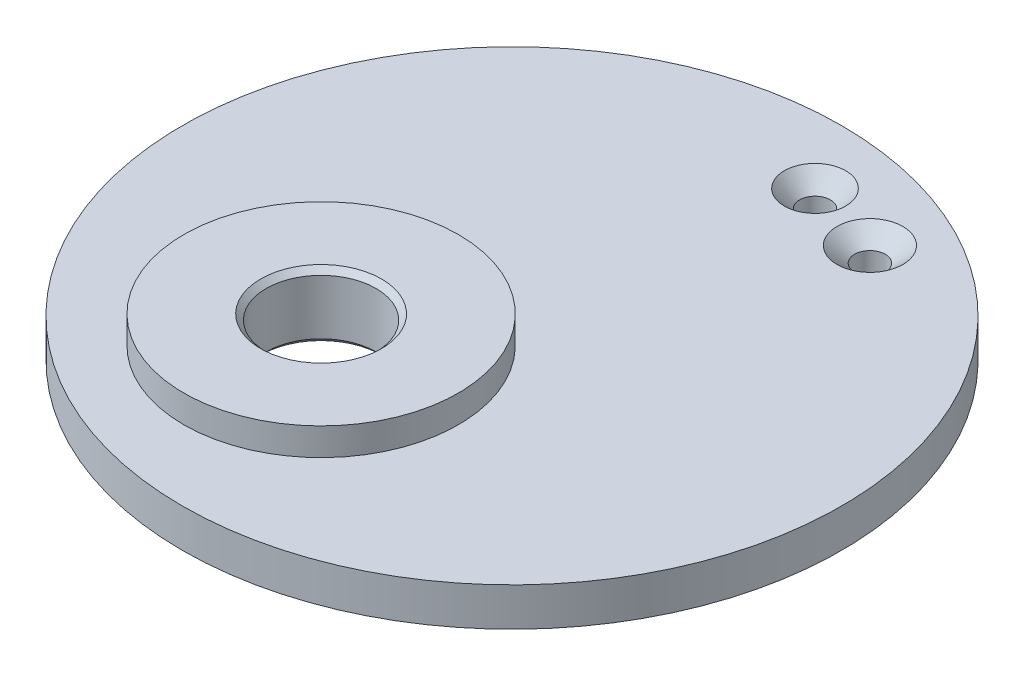
SolidWorks part; units mm, degrees
material "ABS"
ref_plane "Front" through (0, 0, 0) normal (0, 0, 1) x (1, 0, 0)
ref_plane "Top" through (0, 0, 0) normal (0, 1, 0) x (1, 0, 0)
ref_plane "Right" through (0, 0, 0) normal (1, 0, 0) x (0, 0, -1)
sketch "Sketch1" plane through (0, 0, 0) normal (0, 1, 0) x (1, 0, 0)
  circle A0 centre (0, 0) radius 38.1
  dimension "D1" = 76.2
extrude "Boss-Extrude1" add sketch "Sketch1" along normal blind 4.445
sketch "Sketch2" plane through (0, 4.445, 0) normal (0, 1, 0) x (1, 0, 0)
  circle A1 centre (-8.06, -14.01) radius 14.4145
  circle A6 centre (4.76, 30.27) radius 1.778
  circle A7 centre (13.65, 27.73) radius 1.778
  dimension "D1" = 27.73
  dimension "D3" = 3.556
  dimension "D6" = 3.556
  dimension "D9" = 28.829
  dimension "D2" = 13.65
  dimension "D4" = 30.27
  dimension "D5" = 4.76
  dimension "D7" = 14.01
  dimension "D8" = 8.06
extrude "Cut-Extrude1" cut sketch "Sketch2" against normal through all both and the other way through all
sketch "Sketch3" plane through (0, 0, 0) normal (0, -1, 0) x (1, 0, 0)
  arc A0 (4.76, -30.27) -> (13.65, -27.73) centre (7.3136, -22.3803) ccw construction
  arc A1 (3.1957, -35.1031) -> (17.5316, -31.0072) centre (7.3136, -22.3803) ccw
  arc A2 (6.3243, -25.4369) -> (9.7684, -24.4528) centre (7.3136, -22.3803) ccw
  arc A3 (6.3243, -25.4369) -> (3.1957, -35.1031) centre (4.76, -30.27) ccw
  arc A4 (17.5316, -31.0072) -> (9.7684, -24.4528) centre (13.65, -27.73) ccw
  point P3 (9.5918, -30.3539)
  dimension "D1" = 5.08
extrude "Cut-Extrude2" [suppressed] cut sketch "Sketch3" against normal blind 1.905
sketch "Sketch8" plane through (0, 4.445, 0) normal (0, 1, 0) x (1, 0, 0)
  line L0 (0, 0) -> (0, -38.1) construction
  line L1 (-13.97, -38.1) -> (13.97, -38.1)
  line L2 (-13.97, -38.1) -> (-13.97, -64.008)
  line L3 (-13.97, -64.008) -> (13.97, -64.008)
  line L4 (13.97, -38.1) -> (13.97, -64.008)
  line L5 (-20.32, -70.358) -> (-20.32, -32.229)
  line L6 (-20.32, -32.229) -> (20.32, -32.229)
  line L7 (20.32, -32.229) -> (20.32, -70.358)
  line L8 (20.32, -70.358) -> (-20.32, -70.358)
  circle A0 centre (0, 0) radius 38.1 construction
  dimension "D1" = 27.94
  dimension "D2" = 25.908
  dimension "D3" = 6.35
  dimension "D4" = 6.35
extrude "Boss-Extrude4" [suppressed] add sketch "Sketch8" against normal up to surface (6.35 mm away)
fillet "Fillet4" [suppressed] radius 6.35
sketch "Sketch9" plane through (0, 4.445, 0) normal (0, 1, 0) x (1, 0, 0)
  line L0 (22.86, -6.35) -> (22.86, -16.51) construction
  line L1 (27.6225, -6.35) -> (27.6225, -16.51)
  line L2 (18.0975, -6.35) -> (18.0975, -16.51)
  arc A0 (27.6225, -6.35) -> (18.0975, -6.35) centre (22.86, -6.35) ccw
  arc A1 (18.0975, -16.51) -> (27.6225, -16.51) centre (22.86, -16.51) ccw
  point P2 (22.86, -11.43)
  dimension "D1" = 9.525
  dimension "D2" = 11.43
  dimension "D3" = 22.86
  dimension "D4" = 10.16
extrude "Cut-Extrude3" [suppressed] cut sketch "Sketch9" against normal through all both and the other way through all
chamfer "Chamfer1" distance 2.032 angle 41 2 edges at (4.76, 4.445, -28.492) (13.65, 4.445, -25.952)
sketch "Sketch10" plane through (0, 0, 0) normal (0, -1, 0) x (1, 0, 0)
  circle A0 centre (-8.06, 14.01) radius 15.875
  circle A1 centre (-8.06, 14.01) radius 6.35
  dimension "D1" = 31.75
  dimension "D2" = 12.7
extrude "Boss-Extrude5" add sketch "Sketch10" against normal blind 7.62
chamfer "Chamfer2" distance 0.635 angle 45 2 edges at (-8.06, 0, 7.66) (-8.06, 7.62, 7.66)
